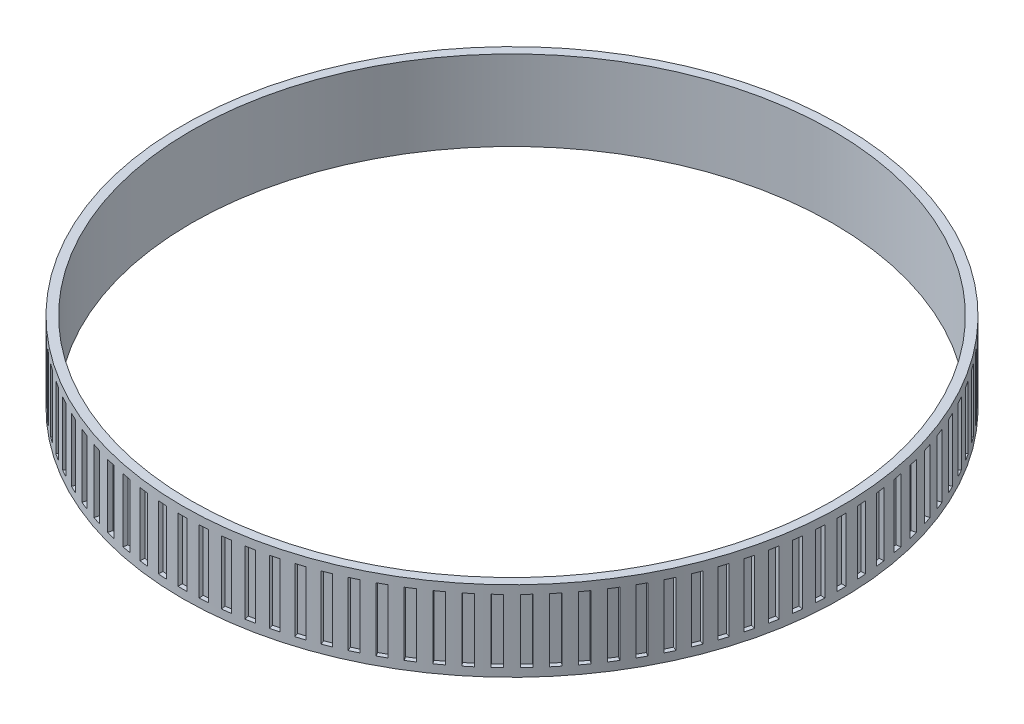
SolidWorks part; units mm, degrees
material "Plain Carbon Steel"
ref_plane "Front Plane" through (0, 0, 0) normal (0, 0, 1) x (1, 0, 0)
ref_plane "Top Plane" through (0, 0, 0) normal (0, 1, 0) x (1, 0, 0)
ref_plane "Right Plane" through (0, 0, 0) normal (1, 0, 0) x (0, 0, -1)
sketch "Sketch1" plane through (0, 0, 0) normal (0, 0, 1) x (1, 0, 0)
  line L0 (0, 4.5) -> (37, 4.5) construction
  line L1 (0, 0) -> (1, 0)
  line L2 (0, 0) -> (0, 9)
  line L3 (0, 9) -> (1, 9)
  line L4 (1, 0) -> (1, 9)
  line L5 (37, 9.7871) -> (37, 0) construction
  dimension "D1" = 9
  dimension "D2" = 1
revolve "Revolve1" add sketch "Sketch1" angle 360 about L5
sketch "Sketch3" plane through (0, 0, 0) normal (0, 0, 1) x (1, 0, 0)
  line L0 (0, 9) -> (0, 0) construction
  line L1 (-0.5, 0.9401) -> (0.5, 0.9401)
  line L2 (-0.5, 0.9401) -> (-0.5, 8.0599)
  line L3 (-0.5, 8.0599) -> (0.5, 8.0599)
  line L4 (0.5, 0.9401) -> (0.5, 8.0599)
  line L5 (-0.5, 0.9401) -> (0.5, 8.0599) construction
  line L6 (-0.5, 8.0599) -> (0.5, 0.9401) construction
  point P0 (0, 4.5)
  dimension "D1" = 1
extrude "Cut-Extrude1" cut sketch "Sketch3" against normal mid plane 1
pattern_circular "CirPattern1" count 100 over 360 about axis through (37, 0, 0) along (0, 1, 0) of "Cut-Extrude1"
